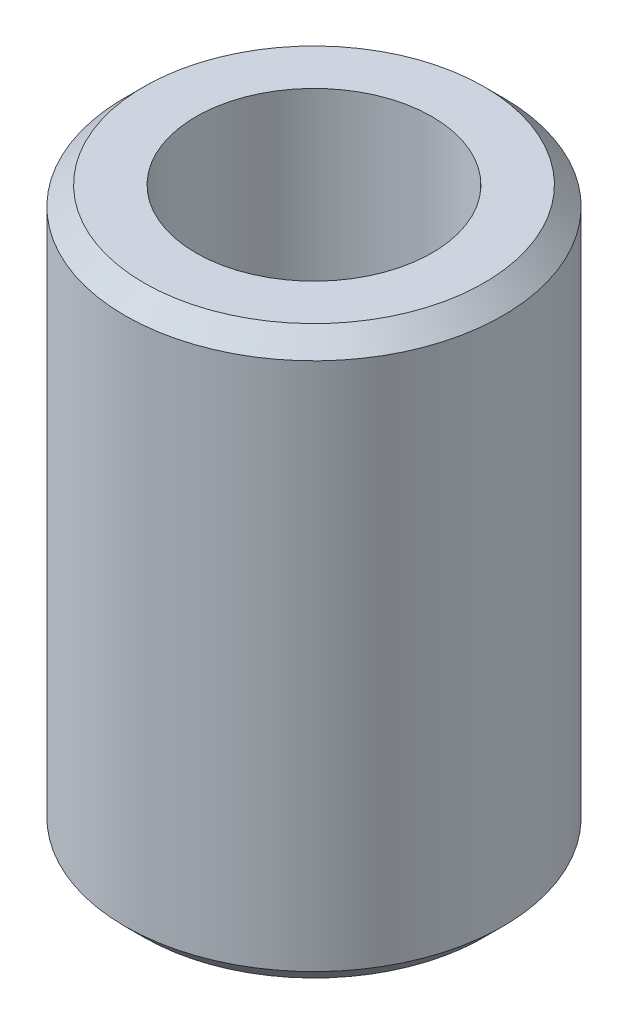
SolidWorks part; units mm, degrees
ref_plane "Front Plane" through (0, 0, 0) normal (0, 0, 1) x (1, 0, 0)
ref_plane "Top Plane" through (0, 0, 0) normal (0, 1, 0) x (1, 0, 0)
ref_plane "Right Plane" through (0, 0, 0) normal (1, 0, 0) x (0, 0, -1)
sketch "Sketch1" plane through (0, 0, 0) normal (0, 1, 0) x (1, 0, 0)
  circle A0 centre (0, 0) radius 20
  circle A1 centre (0, 0) radius 12.5
  dimension "D1" = 25
  dimension "D2" = 40
extrude "Boss-Extrude1" add sketch "Sketch1" along normal mid plane 60
chamfer "Chamfer1" distance 2 angle 45 2 edges at (0, -30, 20) (0, 30, 20)
